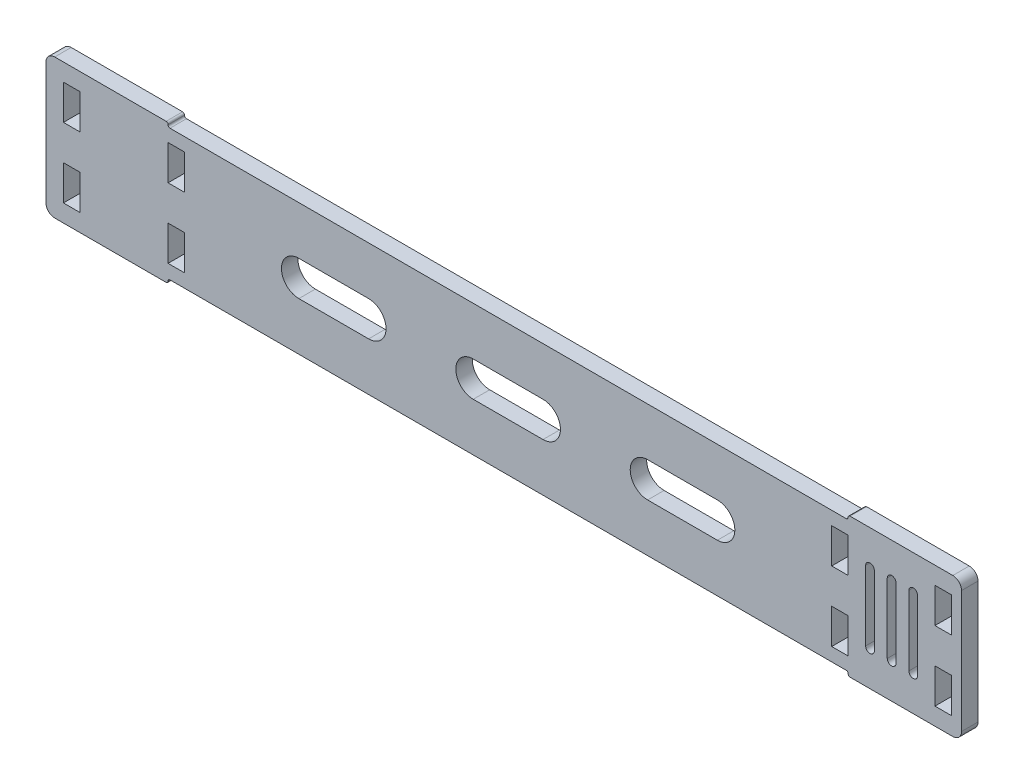
SolidWorks part; units mm, degrees
ref_plane "Front Plane" through (0, 0, 0) normal (0, 0, 1) x (1, 0, 0)
ref_plane "Top Plane" through (0, 0, 0) normal (0, 1, 0) x (1, 0, 0)
ref_plane "Right Plane" through (0, 0, 0) normal (1, 0, 0) x (0, 0, -1)
sketch "Sketch1" plane through (0, 0, 0) normal (0, 0, 1) x (1, 0, 0)
  line L0 (-18.6944, 19.05) -> (-18.6944, 6.35)
  line L1 (0, 0) -> (-304.8, 0)
  line L2 (0, 0) -> (0, 50.8)
  line L3 (0, 50.8) -> (-304.8, 50.8)
  line L4 (-304.8, 0) -> (-304.8, 50.8)
  line L5 (-18.6944, 44.45) -> (-12.7, 44.45)
  line L6 (-18.6944, 44.45) -> (-18.6944, 31.75)
  line L7 (-18.6944, 31.75) -> (-12.7, 31.75)
  line L8 (-12.7, 44.45) -> (-12.7, 31.75)
  line L9 (-18.6944, 19.05) -> (-12.7, 19.05)
  line L10 (-12.7, 19.05) -> (-12.7, 6.35)
  line L11 (-18.6944, 6.35) -> (-12.7, 6.35)
  line L12 (-260.35, 31.75) -> (-254.3556, 31.75)
  line L13 (-260.35, 44.45) -> (-260.35, 31.75)
  line L14 (-260.35, 44.45) -> (-254.3556, 44.45)
  line L15 (-254.3556, 44.45) -> (-254.3556, 31.75)
  line L16 (-260.35, 19.05) -> (-254.3556, 19.05)
  line L17 (-260.35, 19.05) -> (-260.35, 6.35)
  line L18 (-260.35, 6.35) -> (-254.3556, 6.35)
  line L19 (-254.3556, 19.05) -> (-254.3556, 6.35)
  line L20 (-292.4556, 19.05) -> (-292.4556, 6.35)
  line L21 (-298.45, 6.35) -> (-292.4556, 6.35)
  line L22 (-298.45, 19.05) -> (-298.45, 6.35)
  line L23 (-298.45, 19.05) -> (-292.4556, 19.05)
  line L24 (-298.45, 31.75) -> (-292.4556, 31.75)
  line L25 (-298.45, 44.45) -> (-298.45, 31.75)
  line L26 (-298.45, 44.45) -> (-292.4556, 44.45)
  line L27 (-292.4556, 44.45) -> (-292.4556, 31.75)
  dimension "D1" = 50.8
  dimension "D2" = 304.8
  dimension "D3" = 5.9944
  dimension "D4" = 12.7
  dimension "D5" = 6.35
  dimension "D7" = 12.7
  dimension "D9" = 44.45
  dimension "D6" = 2
  dimension "D8" = 2
  dimension "D10" = 2
extrude "Boss-Extrude1" add sketch "Sketch1" along normal blind 5.9944
sketch "Sketch3" plane through (0, 0, 5.9944) normal (0, 0, 1) x (1, 0, 0)
  line L0 (0, 50.8) -> (-304.8, 50.8) construction
  line L1 (-260.35, 50.8) -> (-12.7, 50.8)
  line L2 (-260.35, 50.8) -> (-260.35, 49.3125)
  line L3 (-260.35, 49.3125) -> (-12.7, 49.3125)
  line L4 (-12.7, 50.8) -> (-12.7, 49.3125)
  line L7 (-260.35, 44.45) -> (-260.35, 31.75) construction
  line L8 (-12.7, 31.75) -> (-12.7, 44.45) construction
  line L9 (-304.8, 25.4) -> (0, 25.4) construction
  line L10 (-304.8, 50.8) -> (-304.8, 0) construction
  line L11 (0, 0) -> (0, 50.8) construction
  line L12 (-12.7, 0) -> (-12.7, 1.4875)
  line L13 (-260.35, 1.4875) -> (-12.7, 1.4875)
  line L14 (-260.35, 0) -> (-260.35, 1.4875)
  line L15 (-260.35, 0) -> (-12.7, 0)
  dimension "D1" = 1.4875
extrude "Cut-Extrude3" cut sketch "Sketch3" against normal through all
fillet "Fillet4" radius 0.7 8 edges at (-12.7, 50.8, 2.9972) (-12.7, 49.3125, 2.9972) (-260.35, 50.8, 2.9972) (-260.35, 49.3125, 2.9972) (-260.35, 0, 2.9972) (-260.35, 1.4875, 2.9972) (-12.7, 0, 2.9972) (-12.7, 1.4875, 2.9972)
sketch "Sketch4" plane through (0, 0, 5.9944) normal (0, 0, 1) x (1, 0, 0)
  line L1 (0, 50.8) -> (28.575, 50.8)
  line L2 (0, 50.8) -> (0, 0)
  line L3 (0, 0) -> (28.575, 0)
  line L4 (28.575, 50.8) -> (28.575, 0)
  dimension "D1" = 28.575
extrude "Boss-Extrude2" add sketch "Sketch4" against normal up to surface (5.9944 mm away) up to face at (-139.7, 25.4, 0)
sketch "Sketch5" plane through (0, 0, 5.9944) normal (0, 0, 1) x (1, 0, 0)
  line L0 (-12.7, 44.45) -> (28.575, 44.45) construction
  line L1 (28.575, 0) -> (28.575, 50.8) construction
  line L2 (-12.7, 6.35) -> (28.575, 6.35) construction
  line L3 (-12.7, 6.35) -> (-12.7, 19.05) construction
  line L4 (-18.6944, 6.35) -> (-12.7, 6.35) construction
  line L5 (-12.7, 19.05) -> (28.575, 19.05) construction
  line L6 (-12.7, 31.75) -> (28.575, 31.75) construction
  line L8 (18.8961, 44.45) -> (24.8905, 44.45)
  line L9 (18.8961, 44.45) -> (18.8961, 31.75)
  line L10 (18.8961, 31.75) -> (24.8905, 31.75)
  line L11 (24.8905, 44.45) -> (24.8905, 31.75)
  line L12 (18.8961, 19.05) -> (24.8905, 19.05)
  line L13 (18.8961, 19.05) -> (18.8961, 6.35)
  line L14 (18.8961, 6.35) -> (24.8905, 6.35)
  line L15 (24.8905, 19.05) -> (24.8905, 6.35)
  dimension "D1" = 5.9944
  dimension "D2" = 5.9944
  dimension "D3" = 3.6845
  dimension "D4" = 3.6845
extrude "Cut-Extrude4" cut sketch "Sketch5" against normal through all
fillet "Fillet5" radius 3.175 4 edges at (-304.8, 50.8, 2.9972) (-304.8, 0, 2.9972) (28.575, 0, 2.9972) (28.575, 50.8, 2.9972)
sketch "Sketch6" plane through (0, 0, 5.9944) normal (0, 0, 1) x (1, 0, 0)
  line L0 (-136.525, 49.3125) -> (-136.525, 1.4875) construction
  line L1 (-259.65, 49.3125) -> (-13.4, 49.3125) construction
  line L2 (-13.4, 1.4875) -> (-259.65, 1.4875) construction
  line L3 (-123.825, 25.4) -> (-149.225, 25.4) construction
  line L4 (-123.825, 19.05) -> (-149.225, 19.05)
  line L5 (-123.825, 31.75) -> (-149.225, 31.75)
  line L6 (-60.325, 25.4) -> (-85.725, 25.4) construction
  line L7 (-60.325, 19.05) -> (-85.725, 19.05)
  line L8 (-60.325, 31.75) -> (-85.725, 31.75)
  line L9 (-187.325, 25.4) -> (-212.725, 25.4) construction
  line L10 (-187.325, 19.05) -> (-212.725, 19.05)
  line L11 (-187.325, 31.75) -> (-212.725, 31.75)
  arc A0 (-123.825, 19.05) -> (-123.825, 31.75) centre (-123.825, 25.4) ccw
  arc A1 (-149.225, 31.75) -> (-149.225, 19.05) centre (-149.225, 25.4) ccw
  arc A2 (-60.325, 19.05) -> (-60.325, 31.75) centre (-60.325, 25.4) ccw
  arc A3 (-85.725, 31.75) -> (-85.725, 19.05) centre (-85.725, 25.4) ccw
  arc A4 (-187.325, 19.05) -> (-187.325, 31.75) centre (-187.325, 25.4) ccw
  arc A5 (-212.725, 31.75) -> (-212.725, 19.05) centre (-212.725, 25.4) ccw
  point P8 (-136.525, 25.4)
  point P16 (-73.025, 25.4)
  point P23 (-200.025, 25.4)
  dimension "D2" = 6.35
  dimension "D1" = 25.4
  dimension "D3" = 2
  dimension "D4" = 2
extrude "Cut-Extrude5" cut sketch "Sketch6" against normal through all
sketch "Sketch7" plane through (0, 0, 5.9944) normal (0, 0, 1) x (1, 0, 0)
  line L0 (28.575, 25.4) -> (-19.5215, 25.4) construction
  line L1 (28.575, 3.175) -> (28.575, 47.625) construction
  line L2 (-4.7625, 12.7) -> (-4.7625, 38.1) construction
  line L3 (-6.35, 12.7) -> (-6.35, 38.1)
  line L4 (-3.175, 12.7) -> (-3.175, 38.1)
  line L5 (-12.7, 31.75) -> (-12.7, 44.45) construction
  line L6 (3.1115, 12.7) -> (3.1115, 38.1) construction
  line L7 (1.524, 12.7) -> (1.524, 38.1)
  line L8 (4.699, 12.7) -> (4.699, 38.1)
  line L9 (10.9855, 12.7) -> (10.9855, 38.1) construction
  line L10 (9.398, 12.7) -> (9.398, 38.1)
  line L11 (12.573, 12.7) -> (12.573, 38.1)
  arc A0 (-6.35, 12.7) -> (-3.175, 12.7) centre (-4.7625, 12.7) ccw
  arc A1 (-3.175, 38.1) -> (-6.35, 38.1) centre (-4.7625, 38.1) ccw
  arc A2 (1.524, 12.7) -> (4.699, 12.7) centre (3.1115, 12.7) ccw
  arc A3 (4.699, 38.1) -> (1.524, 38.1) centre (3.1115, 38.1) ccw
  arc A4 (9.398, 12.7) -> (12.573, 12.7) centre (10.9855, 12.7) ccw
  arc A5 (12.573, 38.1) -> (9.398, 38.1) centre (10.9855, 38.1) ccw
  point P6 (-4.7625, 25.4)
  point P16 (3.1115, 25.4)
  point P23 (10.9855, 25.4)
  dimension "D2" = 1.5875
  dimension "D1" = 25.4
  dimension "D3" = 6.35
  dimension "D4" = 3
extrude "Cut-Extrude6" cut sketch "Sketch7" against normal through all
